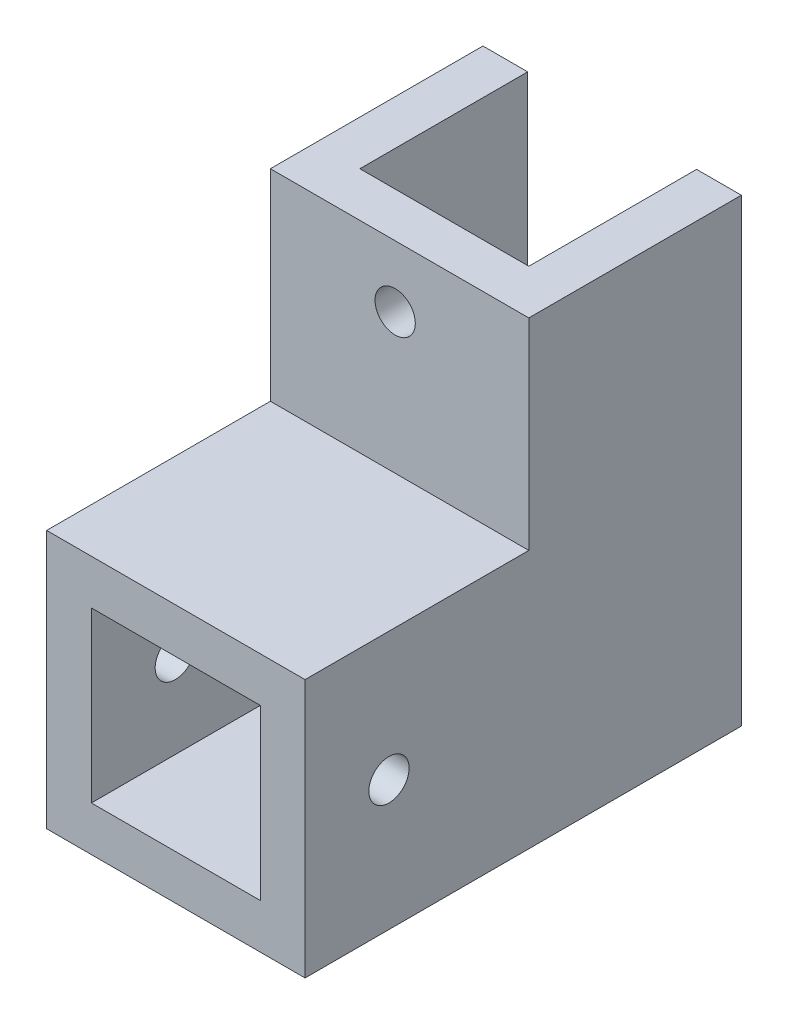
SolidWorks part; units mm, degrees
ref_plane "前视基准面" through (0, 0, 0) normal (0, 0, 1) x (1, 0, 0)
ref_plane "上视基准面" through (0, 0, 0) normal (0, 1, 0) x (1, 0, 0)
ref_plane "右视基准面" through (0, 0, 0) normal (1, 0, 0) x (0, 0, -1)
sketch "草图1" plane through (0, 0, 0) normal (0, 1, 0) x (1, 0, 0)
  line L1 (-11.1538, 14.2692) -> (-7.1538, 14.2692)
  line L2 (-11.1538, 14.2692) -> (-11.1538, -4.7308)
  line L3 (-11.1538, -4.7308) -> (-7.3846, -4.7308)
  line L4 (-7.1538, 14.2692) -> (-7.1538, -0.7308)
  line L5 (-7.3846, -4.7308) -> (11.9462, -4.7308)
  line L7 (-7.1538, -0.7308) -> (7.9462, -0.7308)
  line L8 (11.9462, -4.7308) -> (11.9462, -0.7308)
  line L10 (11.9462, -0.7308) -> (11.9462, 14.2692)
  line L11 (11.9462, 14.2692) -> (7.9462, 14.2692)
  line L12 (7.9462, -0.7308) -> (7.9462, 14.2692)
  dimension "D1" = 15
  dimension "D2" = 15
  dimension "D3" = 4
  dimension "D4" = 4
  dimension "D5" = 4
  dimension "D6" = 15.1
extrude "凸台-拉伸1" add sketch "草图1" along normal blind 20
sketch "草图2" plane through (0, 0, 0.7308) normal (0, 0, -1) x (-1, 0, 0)
  line L0 (7.1538, 20) -> (7.1538, 0) construction
  line L1 (-11.9462, 0) -> (11.1538, 0)
  line L2 (-11.9462, 0) -> (-11.9462, -23.1)
  line L3 (-11.9462, -23.1) -> (11.1538, -23.1)
  line L4 (11.1538, 0) -> (11.1538, -23.1)
  line L5 (-7.9462, -4) -> (7.1538, -4)
  line L6 (-7.9462, -4) -> (-7.9462, -19.1)
  line L7 (-7.9462, -19.1) -> (7.1538, -19.1)
  line L8 (7.1538, -4) -> (7.1538, -19.1)
  line L9 (-7.9462, 0) -> (7.1538, 0) construction
  dimension "D1" = 15.1
  dimension "D2" = 15.1
  dimension "D3" = 4
  dimension "D4" = 4
  dimension "D5" = 4
  dimension "D6" = 4
  dimension "D7" = 0
  dimension "D8" = 0
extrude "凸台-拉伸2" add sketch "草图2" against normal blind 24
sketch "草图3" plane through (0, 0, 0.7308) normal (0, 0, -1) x (-1, 0, 0)
  line L0 (-11.9462, -23.1) -> (11.1538, -23.1) construction
  line L1 (-11.9462, 0) -> (-7.9462, 0)
  line L2 (-11.9462, 0) -> (-11.9462, -23.1)
  line L3 (-11.9462, -23.1) -> (-7.9462, -23.1)
  line L4 (-7.9462, 0) -> (-7.9462, -23.1)
  line L6 (11.1538, 0) -> (7.1538, 0)
  line L7 (11.1538, 0) -> (11.1538, -23.1)
  line L8 (11.1538, -23.1) -> (7.1538, -23.1)
  line L9 (7.1538, 0) -> (7.1538, -23.1)
  dimension "D1" = 4
  dimension "D2" = 4
extrude "凸台-拉伸3" add sketch "草图3" along normal blind 15
sketch "草图4" plane through (0, 0, 4.7308) normal (0, 0, 1) x (1, 0, 0)
  line L0 (-11.1538, 20) -> (11.9462, 20) construction
  circle A0 centre (0, 12.5) radius 1.8
  dimension "D1" = 3.6
  dimension "D2" = 7.5
extrude "切除-拉伸1" cut sketch "草图4" against normal blind 15
sketch "草图5" plane through (11.9462, 0, 0) normal (1, 0, 0) x (0, 0, -1)
  line L0 (-24.7308, 0) -> (-24.7308, -23.1) construction
  circle A0 centre (-17.2308, -11.5) radius 1.8
  dimension "D1" = 3.6
  dimension "D2" = 7.5
extrude "切除-拉伸2" cut sketch "草图5" against normal blind 35
sketch "草图6" plane through (0, 20, 0) normal (0, 1, 0) x (1, 0, 0)
  line L1 (-11.1538, 14.2692) -> (11.9462, 14.2692)
  line L2 (-11.1538, 14.2692) -> (-11.1538, -4.7308)
  line L3 (-11.1538, -4.7308) -> (11.9462, -4.7308)
  line L4 (11.9462, 14.2692) -> (11.9462, -4.7308)
extrude "切除-拉伸3" cut sketch "草图6" against normal blind 2
